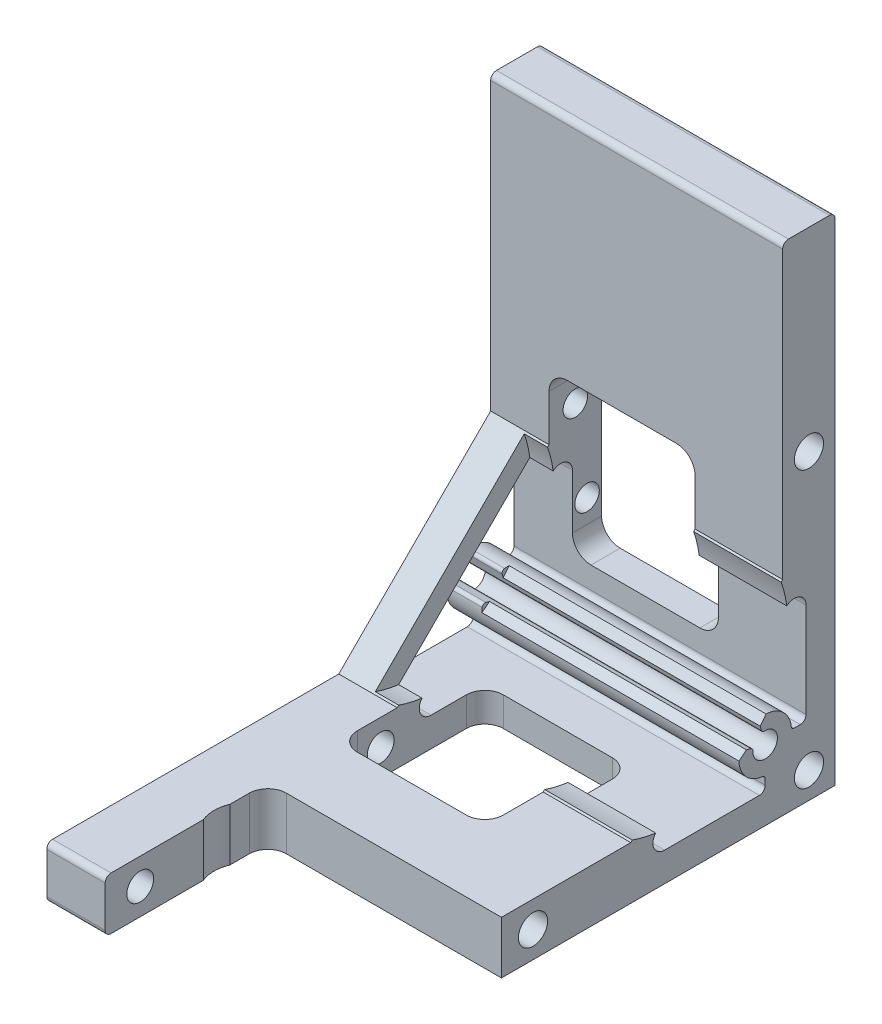
SolidWorks part; units mm, degrees
material "1060 Alloy"
ref_plane "Front Plane" through (0, 0, 0) normal (0, 0, 1) x (1, 0, 0)
ref_plane "Top Plane" through (0, 0, 0) normal (0, 1, 0) x (1, 0, 0)
ref_plane "Right Plane" through (0, 0, 0) normal (1, 0, 0) x (0, 0, -1)
sketch "Sketch1" plane through (0, 0, 0) normal (0, 0, 1) x (1, 0, 0)
  line L0 (-25, 0) -> (25, 0)
  line L1 (0, 0) -> (0, 23.7603) construction
  dimension "D1" = 50
other "Structural Member1"
ref_plane "Plane2" through (-25, 0, 0) normal (1, 0, 0) x (0, 1, 0)
sketch "Sketch14" plane through (-25, 0, 0) normal (1, 0, 0) x (0, 1, 0)
  line L2 (-12, -12) -> (72, -12)
  line L3 (-12, 72) -> (-12, -12)
  line L4 (1, -7) -> (17.2218, -7)
  line L5 (-3, 72) -> (-3, 23)
  line L6 (-6, 0) -> (6, 0) construction
  line L7 (-7, 1) -> (-7, 17.2219)
  line L8 (0, 6) -> (0, -6) construction
  line L9 (0, -4.9749) -> (0, -6)
  line L10 (-4.9749, 0) -> (-6, 0)
  line L11 (0.6604, 2.4645) -> (1.0272, 3.8334)
  line L12 (2.4645, 0.6604) -> (3.8334, 1.0272)
  line L13 (-11, 73) -> (-4, 73)
  line L14 (73, -4) -> (73, -11)
  line L16 (23, -3) -> (72, -3)
  line L18 (-3, 23) -> (23, -3)
  line L19 (-3.5858, 18.6361) -> (18.636, -3.5858)
  arc A0 (0, -6) -> (1, -7) centre (1, -6) ccw
  arc A1 (0.45, -4.4774) -> (0, -4.9749) centre (0.5, -4.9749) ccw
  arc A2 (0.6122, 4.4582) -> (-4.4774, 0.45) centre (0, 0) ccw
  arc A3 (0.1433, 2.0951) -> (2.0951, 0.1433) centre (0, 0) ccw
  arc A4 (-7, 1) -> (-6, 0) centre (-6, 1) ccw
  arc A5 (-4.9749, 0) -> (-4.4774, 0.45) centre (-4.9749, 0.5) ccw
  arc A6 (0.45, -4.4774) -> (4.4582, 0.6122) centre (0, 0) ccw
  arc A7 (4.4582, 0.6122) -> (3.8334, 1.0272) centre (3.9628, 0.5442) ccw
  arc A8 (1.0272, 3.8334) -> (0.6122, 4.4582) centre (0.5442, 3.9628) ccw
  arc A9 (-11, 73) -> (-12, 72) centre (-11, 72) ccw
  arc A10 (-3, 72) -> (-4, 73) centre (-4, 72) ccw
  arc A11 (72, -12) -> (73, -11) centre (72, -11) ccw
  arc A12 (73, -4) -> (72, -3) centre (72, -4) ccw
  arc A13 (0.1433, 2.0951) -> (0.6604, 2.4645) centre (0.1774, 2.5939) ccw
  arc A14 (2.4645, 0.6604) -> (2.0951, 0.1433) centre (2.5939, 0.1774) ccw
  arc A15 (-3.5858, 18.6361) -> (-7, 17.2219) centre (-5, 17.2219) ccw
  arc A16 (17.2218, -7) -> (18.636, -3.5858) centre (17.2218, -5) ccw
  point P0 (0, 0)
sketch "Sketch15" plane through (25, 0, 0) normal (1, 0, 0) x (0, 0, -1)
  line L0 (-72, -12) -> (12, -12) construction
  line L1 (12, 45.15) -> (3, 45.15) construction
  line L2 (12, 45.15) -> (12, 73) construction
  line L3 (12, 73) -> (3, 73) construction
  line L4 (3, 45.15) -> (3, 73) construction
  line L5 (-73, -12) -> (-45.15, -12)
  line L6 (-73, -12) -> (-73, -3)
  line L7 (-73, -3) -> (-45.15, -3)
  line L8 (-45.15, -12) -> (-45.15, -3)
  line L9 (12, -12) -> (12, 72) construction
  line L10 (-73, -4) -> (-73, -11) construction
  line L11 (11, 73) -> (4, 73) construction
  line L12 (-23, -3) -> (-72, -3) construction
  line L13 (3, 72) -> (3, 23) construction
  dimension "D1" = 57.15
  dimension "D2" = 57.15
sketch "Sketch16" plane through (25, 0, 0) normal (1, 0, 0) x (0, 0, -1)
  line L0 (7.5, -7.5) -> (7.5, 39.744) construction
  line L1 (7.5, 39.744) -> (-39.744, -7.5) construction
  line L2 (-39.744, -7.5) -> (7.5, -7.5) construction
  line L3 (12, -12) -> (12, 72) construction
  line L4 (3, 72) -> (3, 23) construction
  line L5 (-72, -12) -> (12, -12) construction
  line L6 (-23, -3) -> (-72, -3) construction
  circle A0 centre (7.5, -7.5) radius 2.5
  circle A1 centre (-39.744, -7.5) radius 2.5
  circle A2 centre (7.5, 39.744) radius 2.5
  dimension "D1" = 5
  dimension "D2" = 47.244
extrude "Cut-Extrude2" cut sketch "Sketch16" against normal blind 20
ref_point "Point2"
ref_point "Point3"
ref_plane "Plane4" through (0, 16.122, 16.122) normal (0, 0.7071, 0.7071) x (1, 0, 0)
sketch "Sketch18" plane through (0, 2.9772, 29.2668) normal (0, 0.7071, 0.7071) x (-1, 0, 0)
  line L0 (-25, -18.5896) -> (25, -18.5896) construction
  line L5 (-25, -38.5896) -> (19, -38.5896)
  line L6 (-25, -38.5896) -> (-25, -18.5896)
  line L7 (-25, -18.5896) -> (-60.2097, -18.5896) construction
  line L9 (-25, -36.9743) -> (25, -36.9743) construction
  line L10 (25, -18.5896) -> (30.15, -18.5896) construction
  line L14 (25, -18.5896) -> (-25, -18.5896)
  line L16 (19, -38.5896) -> (19, -21.7646)
  line L17 (19, -21.7646) -> (25, -21.7646)
  line L18 (25, 35.8577) -> (25, 40.8074) construction
  line L20 (25, -21.7646) -> (25, -18.5896)
  line L29 (-25, -0.2048) -> (25, -0.2048) construction
  line L30 (-25, -36.9743) -> (-25, -0.2048) construction
  dimension "D1" = 40
  dimension "D2" = 6
  dimension "D3" = 6.35
revolve "Cut-Revolve1" cut sketch "Sketch18" angle 360 about L7
sketch "Sketch22" plane through (0, 0, -12) normal (0, 0, -1) x (-1, 0, 0)
  line L0 (25, -12) -> (25, 72) construction
  line L1 (11.825, 4.747) -> (-6.825, 4.747)
  line L2 (15, 7.922) -> (15, 30.922)
  line L3 (11.825, 34.097) -> (-6.825, 34.097)
  line L4 (-10, 7.922) -> (-10, 30.922)
  line L5 (25, 11.922) -> (16.5566, 11.922) construction
  line L6 (25, 13.922) -> (25, 9.922) construction
  line L7 (25, 26.922) -> (12.2594, 26.922) construction
  line L8 (25, 28.922) -> (25, 24.922) construction
  arc A0 (15, 30.922) -> (11.825, 34.097) centre (11.825, 30.922) ccw
  arc A1 (-6.825, 34.097) -> (-10, 30.922) centre (-6.825, 30.922) ccw
  arc A2 (-10, 7.922) -> (-6.825, 4.747) centre (-6.825, 7.922) ccw
  arc A3 (11.825, 4.747) -> (15, 7.922) centre (11.825, 7.922) ccw
  dimension "D1" = 3.175
  dimension "D2" = 10
  dimension "D3" = 25
  dimension "D4" = 4
  dimension "D5" = 4
extrude "Cut-Extrude7" cut sketch "Sketch22" against normal up to next
sketch "Sketch23" plane through (-25, 0, 0) normal (-1, 0, 0) x (0, 0, 1)
  circle A0 centre (-9.5, 11.922) radius 2.1
  circle A1 centre (-7.5, 26.922) radius 2.1
  circle A2 centre (-9.5, 11.922) radius 2 construction
  circle A3 centre (-7.5, 26.922) radius 2 construction
  dimension "D1" = 4.2
extrude "Cut-Extrude8" cut sketch "Sketch23" against normal up to next
sketch "Sketch24" plane through (0, -12, 0) normal (0, -1, 0) x (1, 0, 0)
  line L0 (-15, 11.175) -> (-15, -12) construction
  line L1 (6.825, 8) -> (-11.825, 8)
  line L2 (10, 11.175) -> (10, 29.825)
  line L3 (6.825, 33) -> (-11.825, 33)
  line L4 (-15, 11.175) -> (-15, 29.825)
  line L5 (10, 11.175) -> (10, -12) construction
  line L6 (-15, -3) -> (-15, -12) construction
  line L7 (10, -3) -> (10, -12) construction
  line L8 (25, -12) -> (-25, -12) construction
  line L9 (25, 72) -> (25, -12) construction
  line L10 (25, 73) -> (-15, 73)
  line L11 (25, 73) -> (25, 45.15)
  line L12 (25, 45.15) -> (-11.825, 45.15)
  line L13 (-15, 73) -> (-15, 48.325)
  line L14 (25, 73) -> (-25, 73) construction
  line L15 (12.6968, 63) -> (-25, 63) construction
  line L16 (-25, 72) -> (-25, -12) construction
  line L17 (-1.4559, 25.825) -> (-25, 25.825) construction
  arc A0 (6.825, 8) -> (10, 11.175) centre (6.825, 11.175) ccw
  arc A1 (10, 29.825) -> (6.825, 33) centre (6.825, 29.825) ccw
  arc A2 (-11.825, 33) -> (-15, 29.825) centre (-11.825, 29.825) ccw
  arc A3 (-15, 11.175) -> (-11.825, 8) centre (-11.825, 11.175) ccw
  arc A4 (-15, 48.325) -> (-11.825, 45.15) centre (-11.825, 48.325) ccw
  dimension "D1" = 3.175
  dimension "D2" = 3.175
  dimension "D3" = 10
  dimension "D4" = 57.15
  dimension "D5" = 4
  dimension "D6" = 20
  dimension "D7" = 45
extrude "Cut-Extrude9" cut sketch "Sketch24" against normal up to next
sketch "Sketch25" plane through (-15, 0, 0) normal (1, 0, 0) x (0, 0, -1)
  circle A0 centre (-67, -7.5) radius 2.3 construction
  circle A1 centre (-25.825, -7.5) radius 2.3 construction
  circle A2 centre (-67, -7.5) radius 2.3
  circle A3 centre (-25.825, -7.5) radius 2.3
extrude "Cut-Extrude10" cut sketch "Sketch25" against normal up to next
sketch "Sketch26" plane through (0, -12, 0) normal (0, -1, 0) x (1, 0, 0)
  circle A0 centre (-9.455, 53.912) radius 6
  circle A3 centre (-9.455, 53.912) radius 9.5 construction
  dimension "D1" = 12
extrude "Cut-Extrude11" cut sketch "Sketch26" against normal through all
